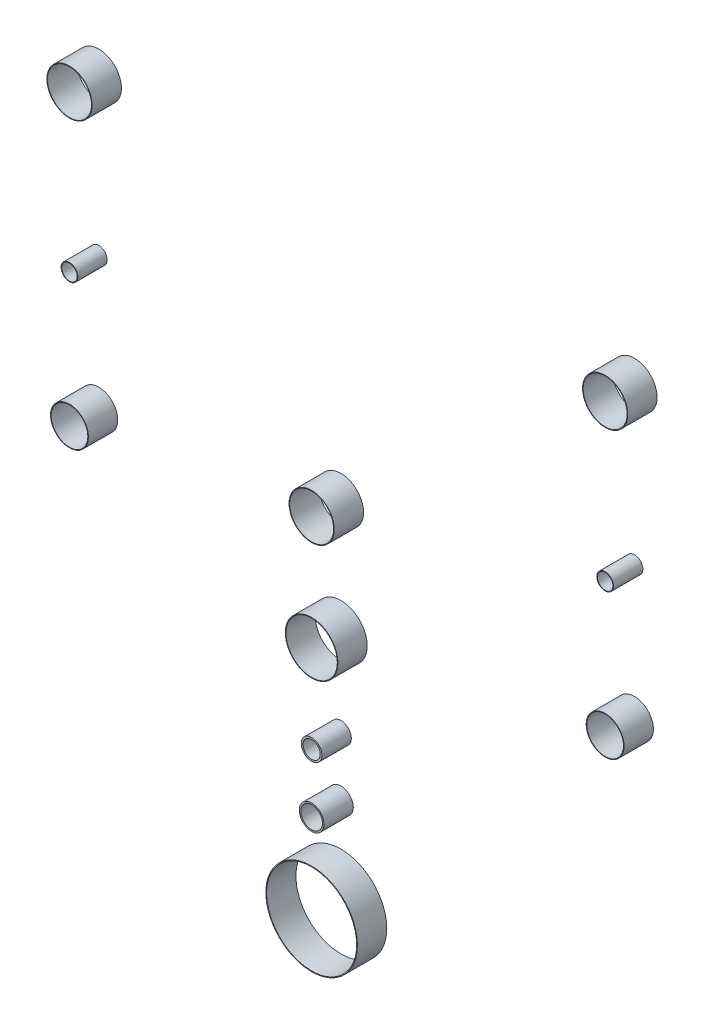
SolidWorks part; units mm, degrees
ref_plane "Front Plane" through (0, 0, 0) normal (0, 0, 1) x (1, 0, 0)
ref_plane "Top Plane" through (0, 0, 0) normal (0, 1, 0) x (1, 0, 0)
ref_plane "Right Plane" through (0, 0, 0) normal (1, 0, 0) x (0, 0, -1)
sketch "Sketch1" plane through (0, 0, 0) normal (0, 0, 1) x (1, 0, 0)
  line L0 (-750, -17917.5696) -> (-750, -11394.1913) construction
  line L1 (-2750, -17917.5696) -> (-2750, -11232.2635) construction
  line L2 (-4400, -17917.5696) -> (-4400, -11500) construction
  line L3 (0, -11500) -> (-10900, -11500) construction
  line L4 (-4900, -17700) -> (-4900, -56390) construction
  line L5 (150, -17700) -> (150, 0) construction
  line L7 (-11050, 0) -> (150, 0) construction
  circle A0 centre (-2750, -16925) radius 312
  circle A1 centre (-2750, -16325) radius 84
  circle A2 centre (-2750, -15925) radius 70.5
  circle A3 centre (-2750, -15325) radius 179
  circle A4 centre (-2750, -14550) radius 154
  circle A5 centre (-750, -12870.9552) radius 154
  circle A6 centre (-750, -13933.0511) radius 57
  circle A7 centre (-750, -14841.3263) radius 129
  circle A8 centre (-2750, -16925) radius 307
  circle A9 centre (-2750, -16325) radius 74
  circle A10 centre (-2750, -15925) radius 58.5
  circle A11 centre (-2750, -15325) radius 175
  circle A12 centre (-2750, -14550) radius 150
  circle A13 centre (-750, -12870.9552) radius 150
  circle A14 centre (-750, -13933.0511) radius 53
  circle A15 centre (-750, -14841.3263) radius 125
  circle A16 centre (-4400, -14841.3263) radius 125
  circle A17 centre (-4400, -14841.3263) radius 129
  circle A18 centre (-4400, -13933.0511) radius 57
  circle A19 centre (-4400, -13933.0511) radius 53
  circle A20 centre (-4400, -12870.9552) radius 154
  circle A21 centre (-4400, -12870.9552) radius 150
  dimension "D5" = 624
  dimension "D7" = 168
  dimension "D8" = 141
  dimension "D11" = 358
  dimension "D12" = 308
  dimension "D16" = 400
  dimension "D17" = 600
  dimension "D18" = 308
  dimension "D20" = 114
  dimension "D21" = 4
  dimension "D22" = 258
  dimension "D1" = 2900
  dimension "D2" = 500
  dimension "D3" = 900
  dimension "D4" = 16925
  dimension "D15" = 600
  dimension "D6" = 5
  dimension "D9" = 10
  dimension "D10" = 12
  dimension "D13" = 4
  dimension "D14" = 4
  dimension "D19" = 4
  dimension "D23" = 4
extrude "Extrude1" add sketch "Sketch1" along normal blind 200
